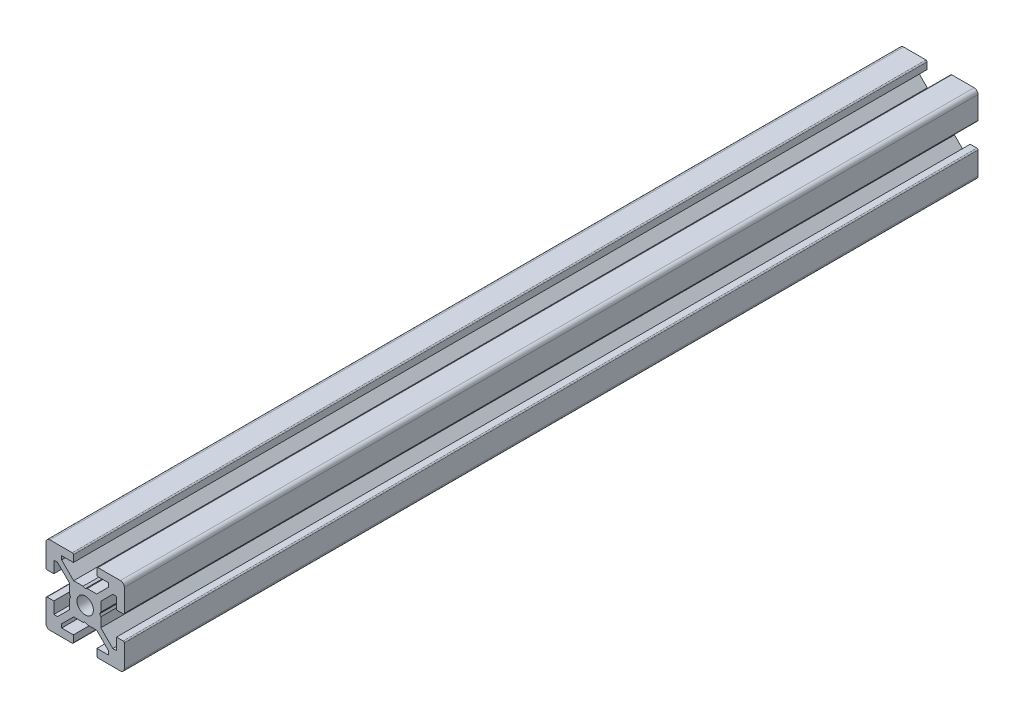
SolidWorks part; units mm, degrees
material "6063-T5"
ref_plane "Front Plane" through (0, 0, 0) normal (0, 0, 1) x (1, 0, 0)
ref_plane "Top Plane" through (0, 0, 0) normal (0, 1, 0) x (1, 0, 0)
ref_plane "Right Plane" through (0, 0, 0) normal (1, 0, 0) x (0, 0, -1)
ref_plane "Plane1" through (0, 0, 0) normal (0, 0, 1) x (1, 0, 0)
sketch "Sketch1" plane through (0, 0, 0) normal (0, 0, 1) x (1, 0, 0)
  line L0 (-10, 9) -> (-10, 3.3)
  line L1 (-9.7, 3) -> (-8, 3)
  line L2 (-8, 3) -> (-8, 6)
  line L3 (-8, 6) -> (-7.0607, 6)
  line L4 (-7.0607, 6) -> (-4, 2.9393)
  line L5 (-4, 2.9393) -> (-4, 0.5196)
  line L6 (-4, 0.5196) -> (-3.7, 0)
  line L7 (-3.7, 0) -> (-4, -0.5196)
  line L8 (-4, -0.5196) -> (-4, -2.9393)
  line L9 (-4, -2.9393) -> (-7.0607, -6)
  line L10 (-7.0607, -6) -> (-8, -6)
  line L11 (-8, -6) -> (-8, -3)
  line L12 (-8, -3) -> (-9.7, -3)
  line L13 (-10, -3.3) -> (-10, -9)
  line L14 (-9, -10) -> (-3.3, -10)
  line L15 (-3, -9.7) -> (-3, -8)
  line L16 (-3, -8) -> (-6, -8)
  line L17 (-6, -8) -> (-6, -7.0607)
  line L18 (-6, -7.0607) -> (-2.9393, -4)
  line L19 (-2.9393, -4) -> (-0.5196, -4)
  line L20 (-0.5196, -4) -> (0, -3.7)
  line L21 (0, -3.7) -> (0.5196, -4)
  line L22 (0.5196, -4) -> (2.9393, -4)
  line L23 (2.9393, -4) -> (6, -7.0607)
  line L24 (6, -7.0607) -> (6, -8)
  line L25 (6, -8) -> (3, -8)
  line L26 (3, -8) -> (3, -9.7)
  line L27 (3.3, -10) -> (9, -10)
  line L28 (10, -9) -> (10, -3.3)
  line L29 (9.7, -3) -> (8, -3)
  line L30 (8, -3) -> (8, -6)
  line L31 (8, -6) -> (7.0606, -6)
  line L32 (7.0606, -6) -> (4, -2.9393)
  line L33 (4, -2.9393) -> (4, -0.5196)
  line L34 (4, -0.5196) -> (3.7, 0)
  line L35 (3.7, 0) -> (4, 0.5196)
  line L36 (4, 0.5196) -> (4, 2.9393)
  line L37 (4, 2.9393) -> (7.0607, 6)
  line L38 (7.0607, 6) -> (8, 6)
  line L39 (8, 6) -> (8, 3)
  line L40 (8, 3) -> (9.7, 3)
  line L41 (10, 3.3) -> (10, 9)
  line L42 (9, 10) -> (3.3, 10)
  line L43 (3, 9.7) -> (3, 8)
  line L44 (3, 8) -> (6, 8)
  line L45 (6, 8) -> (6, 7.0607)
  line L46 (6, 7.0607) -> (2.9393, 4)
  line L47 (2.9393, 4) -> (0.5196, 4)
  line L48 (0.5196, 4) -> (0, 3.7)
  line L49 (0, 3.7) -> (-0.5196, 4)
  line L50 (-0.5196, 4) -> (-2.9394, 4)
  line L51 (-2.9394, 4) -> (-6, 7.0606)
  line L52 (-6, 7.0606) -> (-6, 8)
  line L53 (-6, 8) -> (-3, 8)
  line L54 (-3, 8) -> (-3, 9.7)
  line L55 (-3.3, 10) -> (-9, 10)
  arc A0 (-10, 3.3) -> (-9.7, 3) centre (-9.7, 3.3) ccw
  arc A1 (-9.7, -3) -> (-10, -3.3) centre (-9.7, -3.3) ccw
  arc A2 (-10, -9) -> (-9, -10) centre (-9, -9) ccw
  arc A3 (-3.3, -10) -> (-3, -9.7) centre (-3.3, -9.7) ccw
  arc A4 (3, -9.7) -> (3.3, -10) centre (3.3, -9.7) ccw
  arc A5 (9, -10) -> (10, -9) centre (9, -9) ccw
  arc A6 (10, -3.3) -> (9.7, -3) centre (9.7, -3.3) ccw
  arc A7 (9.7, 3) -> (10, 3.3) centre (9.7, 3.3) ccw
  arc A8 (10, 9) -> (9, 10) centre (9, 9) ccw
  arc A9 (3.3, 10) -> (3, 9.7) centre (3.3, 9.7) ccw
  arc A10 (-3, 9.7) -> (-3.3, 10) centre (-3.3, 9.7) ccw
  arc A11 (-9, 10) -> (-10, 9) centre (-9, 9) ccw
extrude "Boss-Extrude1" add sketch "Sketch1" against normal blind 218
ref_plane "Plane2" through (0, 0, 0) normal (1, 0, 0) x (0, 0, -1)
sketch "Sketch2" plane through (0, 0, 0) normal (1, 0, 0) x (0, 0, -1)
  line L0 (0, 0) -> (0, 2.1)
  line L1 (0, 2.1) -> (407.5, 2.1)
  line L2 (407.5, 2.1) -> (407.5, 0)
  line L3 (407.5, 0) -> (0, 0)
  line L4 (407.5, 0) -> (0, 0) construction
  dimension "D1" = 2.1
  dimension "D2" = 407.5
revolve "Cut-Revolve1" cut sketch "Sketch2" angle 360 about L4
ref_plane "Plane3" through (0, 0, -109) normal (0, 0, 1) x (1, 0, 0)
sketch "Sketch4" plane through (4, 0, 0) normal (1, 0, 0) x (0, 0, -1)
  line L0 (218, 0) -> (0, 0) construction
  line L1 (0, -2.9393) -> (0, -0.5196) construction
  line L2 (109, 2.9393) -> (109, -2.9393) construction
  line L3 (218, 2.9393) -> (0, 2.9393) construction
  line L4 (218, -2.9393) -> (0, -2.9393) construction
  circle A0 centre (10, 0) radius 2.5
  circle A1 centre (208, 0) radius 2.5
  dimension "D1" = 5
  dimension "D2" = 10
extrude "Cut-Extrude1" [suppressed] cut sketch "Sketch4" against normal up to surface (8 mm away)
